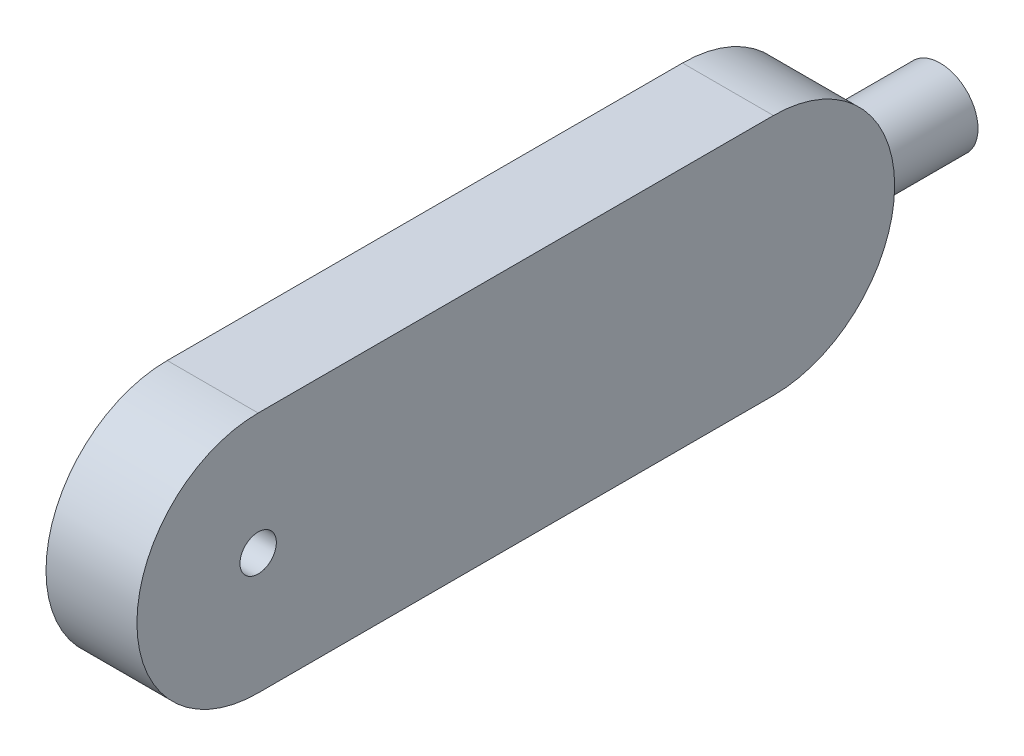
SolidWorks part; units mm, degrees
material "ABS"
ref_plane "Front Plane" through (0, 0, 0) normal (0, 0, 1) x (1, 0, 0)
ref_plane "Top Plane" through (0, 0, 0) normal (0, 1, 0) x (1, 0, 0)
ref_plane "Right Plane" through (0, 0, 0) normal (1, 0, 0) x (0, 0, -1)
sketch "Sketch2" plane through (0, 0, 0) normal (1, 0, 0) x (0, 0, -1)
  line L0 (0, 0) -> (0, 80)
  line L1 (0, 80) -> (250, 80)
  line L3 (250, 0) -> (0, 0)
  line L4 (250, 80) -> (250, 0)
  dimension "D1" = 80
  dimension "D4" = 250
extrude "Boss-Extrude1" add sketch "Sketch2" along normal blind 30
sketch "Sketch11" plane through (30, 0, 0) normal (1, 0, 0) x (0, 0, -1)
  line L0 (0, 40) -> (250, 40) construction
  line L1 (0, 80) -> (0, 0) construction
  line L2 (250, 0) -> (250, 80) construction
  circle A0 centre (40, 40) radius 6
  dimension "D1" = 40
  dimension "D2" = 12
extrude "Cut-Extrude2" cut sketch "Sketch11" against normal through all
sketch "Sketch14" plane through (0, 0, 0) normal (-1, 0, 0) x (0, 0, 1)
  line L0 (-250, 0) -> (-250, 80) construction
  arc A0 (-40, 0) -> (-40, 80) centre (-40, 40) ccw
  arc A1 (-210, 80) -> (-210, 0) centre (-210, 40) ccw
  dimension "D1" = 40
extrude "Cut-Extrude-Thin2" cut sketch "Sketch14" against normal through all thin
sketch "Sketch15" plane through (0, 0, 0) normal (-1, 0, 0) x (0, 0, 1)
  line L0 (-210, 80) -> (-40, 80) construction
  line L1 (-230, 50) -> (-190, 50)
  line L2 (-230, 50) -> (-230, 30)
  line L3 (-230, 30) -> (-190, 30)
  line L4 (-190, 50) -> (-190, 30)
  point P6 (-210, 37.919)
  dimension "D4" = 20
  dimension "D1" = 40
  dimension "D2" = 20
  dimension "D3" = 30
extrude "Cut-Extrude3" cut sketch "Sketch15" against normal blind 25
ref_plane "Plane1" through (0, 0, -230) normal (0, 0, -1) x (-1, 0, 0)
sketch "Sketch16" plane through (0, 0, -230) normal (0, 0, -1) x (-1, 0, 0)
  line L0 (-15, 80) -> (-15, 0) construction
  line L5 (-30, 80) -> (0, 80) construction
  line L6 (-30, 0) -> (0, 0) construction
  circle A0 centre (-15, 40) radius 12.5
  dimension "D1" = 25
extrude "Boss-Extrude2" add sketch "Sketch16" along normal blind 50
